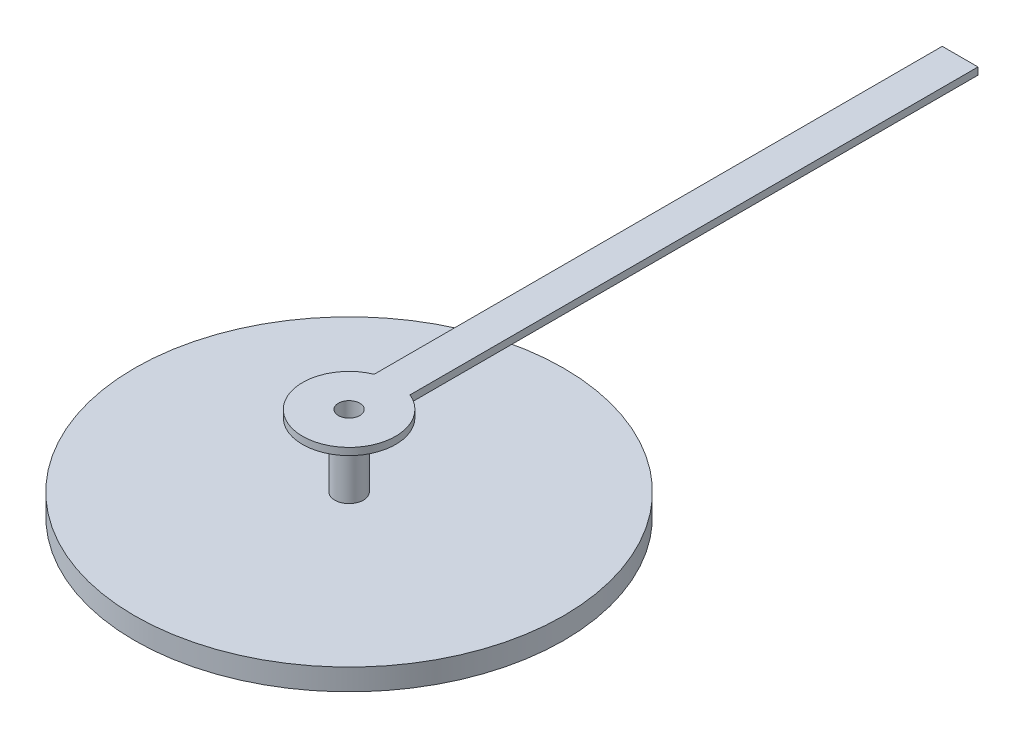
SolidWorks part; units mm, degrees
ref_plane "Front Plane" through (0, 0, 0) normal (0, 0, 1) x (1, 0, 0)
ref_plane "Top Plane" through (0, 0, 0) normal (0, 1, 0) x (1, 0, 0)
ref_plane "Right Plane" through (0, 0, 0) normal (1, 0, 0) x (0, 0, -1)
sketch "Sketch1" plane through (0, 0, 0) normal (0, 1, 0) x (1, 0, 0)
  line L0 (0, 8.4336) -> (0, -94.0328) construction
  line L1 (-2.0666, 0) -> (2.0487, 0) construction
  line L2 (0, 4.5454) -> (0.25, 8.5454) construction
  line L14 (-0.25, 8.5454) -> (0.25, 8.5454)
  line L15 (-0.25, 8.5454) -> (-0.25, 0.6012)
  line L17 (0.25, 8.5454) -> (0.25, 0.6012)
  line L18 (-0.25, 8.5454) -> (0, 4.5454) construction
  arc A0 (-0.25, 0.6012) -> (0.25, 0.6012) centre (0, 0) ccw
  point P7 (0, 4.5454)
  dimension "D1" = 0.5
  dimension "D2" = 0.6511
extrude "Boss-Extrude1" add sketch "Sketch1" along normal blind 0.1
sketch "Sketch2" plane through (0, 0.1, 0) normal (0, -1, 0) x (1, 0, 0)
  circle A0 centre (0, 0) radius 0.2
  dimension "D1" = 0.4
extrude "Boss-Extrude2" add sketch "Sketch2" along normal blind 1
sketch "Sketch3" plane through (0, -0.9, 0) normal (0, -1, 0) x (1, 0, 0)
  circle A0 centre (0, 0) radius 3
  dimension "D1" = 6
extrude "Boss-Extrude3" add sketch "Sketch3" along normal blind 0.3
sketch "Sketch4" plane through (0, 0.1, 0) normal (0, 1, 0) x (1, 0, 0)
  circle A0 centre (0, 0) radius 0.15
  dimension "D1" = 0.3
extrude "Cut-Extrude1" cut sketch "Sketch4" against normal through all
